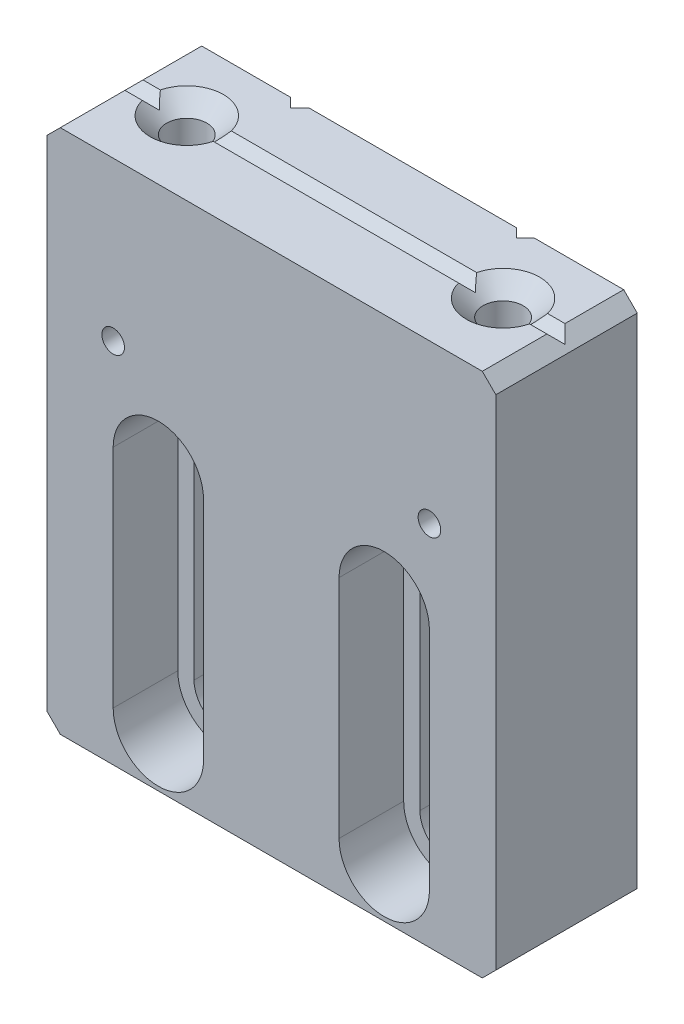
SolidWorks part; units mm, degrees
ref_plane "Front" through (0, 0, 0) normal (0, 0, 1) x (1, 0, 0)
ref_plane "Top" through (0, 0, 0) normal (0, 1, 0) x (1, 0, 0)
ref_plane "Right" through (0, 0, 0) normal (1, 0, 0) x (0, 0, -1)
sketch "Sketch1" plane through (0, 0, 0) normal (0, 0, 1) x (1, 0, 0)
  line L1 (-12.6238, 14.7701) -> (12.6238, 14.7701)
  line L2 (-12.6238, 14.7701) -> (-12.6238, -14.7701)
  line L3 (-12.6238, -14.7701) -> (12.6238, -14.7701)
  line L4 (12.6238, 14.7701) -> (12.6238, -14.7701)
  line L5 (-12.6238, 14.7701) -> (12.6238, -14.7701) construction
  line L6 (-12.6238, -14.7701) -> (12.6238, 14.7701) construction
  point P0 (0, 0)
  dimension "D1" = 29.5402
  dimension "D2" = 25.2476
extrude "Boss-Extrude1" add sketch "Sketch1" along normal blind 7.9502
chamfer "Chamfer1" distance 0.762 angle 45 4 edges at (-12.6238, -14.7701, 3.9751) (12.6238, -14.7701, 3.9751) (-12.6238, 14.7701, 3.9751) (12.6238, 14.7701, 3.9751)
sketch "Sketch2" plane through (0, 14.7701, 0) normal (0, 1, 0) x (1, 0, 0)
  line L0 (-6.35, 0.508) -> (-6.858, 0)
  line L1 (-6.35, 0.508) -> (-5.842, 0)
  line L2 (-6.858, 0) -> (-6.35, -0.508)
  line L3 (-5.842, 0) -> (-6.35, -0.508)
  line L4 (-6.35, 0.508) -> (-6.35, -0.508) construction
  line L5 (-6.858, 0) -> (-5.842, 0) construction
  line L6 (0, 1.7821) -> (0, -2.8787) construction
  line L7 (6.858, 0) -> (5.842, 0) construction
  line L8 (6.35, 0.508) -> (6.35, -0.508) construction
  line L9 (5.842, 0) -> (6.35, -0.508)
  line L10 (6.858, 0) -> (6.35, -0.508)
  line L11 (6.35, 0.508) -> (5.842, 0)
  line L12 (6.35, 0.508) -> (6.858, 0)
  point P1 (-6.35, 0)
  point P7 (6.35, 0)
extrude "Cut-Extrude1" cut sketch "Sketch2" against normal through all
hole_wizard "#4-40 Tapped Hole1" positions "Sketch3" profile "Sketch4" tap size "#4-40" standard "ANSI Inch"
sketch "Sketch3" plane through (0, 14.7701, 0) normal (0, 1, 0) x (1, 0, 0)
  point P0 (-8.89, -3.81)
  point P2 (8.89, -3.81)
sketch "Sketch4" plane through (-8.89, 14.7701, 3.81) normal (1, 0, 0) x (0, 0, 1)
  line L0 (0, 0) -> (0, 10.2296)
  line L1 (0, 10.2296) -> (1.1303, 9.5504)
  line L2 (1.1303, 9.5504) -> (1.1303, 0.9271)
  line L3 (1.1303, 0.9271) -> (2.0574, 0)
  line L5 (2.0574, 0) -> (0, 0)
  line L6 (-1.1303, 0.9271) -> (-2.0574, 0) construction
  line L10 (0, 10.2296) -> (-1.1303, 9.5504) construction
  line L11 (0, -6.35) -> (0, 107.95) construction
  dimension "Tap Drill Dia." = 2.2606
  dimension "Tap Drill Depth" = 9.5504
  dimension "Near C'Sink Dia." = 4.1148
  dimension "Near C'Sink Angle" = 90
  dimension "Drill Angle" = 118
cosmetic thread "Hole Thread1" parameters "D1"=7.62, "D2"=2.8448
cosmetic thread "Hole Thread2" parameters "D1"=7.62, "D2"=2.8448
sketch "Sketch6" plane through (0, 0, 7.9502) normal (0, 0, 1) x (1, 0, 0)
  line L0 (0, 6.9795) -> (0, -15.9132) construction
  line L1 (-7.9756, -12.0015) -> (-4.7244, -12.0015)
  line L2 (-7.9756, -12.0015) -> (-7.9756, 0.6985)
  line L3 (-7.9756, 0.6985) -> (-4.7244, 0.6985)
  line L4 (-4.7244, -12.0015) -> (-4.7244, 0.6985)
  line L5 (4.7244, -12.0015) -> (4.7244, 0.6985)
  line L6 (7.9756, 0.6985) -> (4.7244, 0.6985)
  line L7 (7.9756, -12.0015) -> (7.9756, 0.6985)
  line L8 (7.9756, -12.0015) -> (4.7244, -12.0015)
  circle A0 centre (-6.35, 0.6985) radius 1.6256
  circle A1 centre (-6.35, -12.0015) radius 1.6256
  circle A2 centre (6.35, -12.0015) radius 1.6256
  circle A3 centre (6.35, 0.6985) radius 1.6256
  dimension "D1" = 12.7
  dimension "D2" = 3.2512
extrude "Cut-Extrude3" cut sketch "Sketch6" against normal through all contours A0 | L2 L3 L4 L1 | A1 | A2 | L5 L6 L7 L8 | A3
sketch "Sketch8" plane through (0, 0, 7.9502) normal (0, 0, 1) x (1, 0, 0)
  line L0 (0, 5.5487) -> (0, -16.5065) construction
  line L1 (8.89, -12.0015) -> (3.81, -12.0015)
  line L2 (-8.89, -12.0015) -> (-3.81, -12.0015)
  line L3 (-8.89, -12.0015) -> (-8.89, 0.6985)
  line L4 (-8.89, 0.6985) -> (-3.81, 0.6985)
  line L5 (8.89, 0.6985) -> (3.81, 0.6985)
  line L6 (3.81, -12.0015) -> (3.81, 0.6985)
  line L7 (8.89, -12.0015) -> (8.89, 0.6985)
  line L9 (-3.81, -12.0015) -> (-3.81, 0.6985)
  circle A0 centre (-6.35, 0.6985) radius 2.54
  circle A1 centre (-6.35, -12.0015) radius 2.54
  circle A2 centre (6.35, -12.0015) radius 2.54
  circle A3 centre (6.35, 0.6985) radius 2.54
  dimension "D1" = 12.7
  dimension "D2" = 5.08
extrude "Cut-Extrude4" cut sketch "Sketch8" against normal blind 3.6322
sketch "Sketch11" plane through (0, 0, 7.9502) normal (0, 0, 1) x (1, 0, 0)
  line L0 (0, 0) -> (0, 12.6329) construction
  circle A0 centre (-8.89, 5.8674) radius 0.635
  circle A1 centre (8.89, 5.8674) radius 0.635
extrude "Cut-Extrude5" cut sketch "Sketch11" against normal through all
sketch "Sketch15" plane through (0, 0, 0) normal (1, 0, 0) x (0, 0, -1)
  line L0 (-4.318, 14.7701) -> (-3.81, 14.2621)
  line L1 (-7.9502, 14.7701) -> (0, 14.7701) construction
  line L2 (-3.81, 14.2621) -> (-3.302, 14.7701)
extrude "Cut-Extrude7" cut sketch "Sketch15" against normal through all and the other way through all
